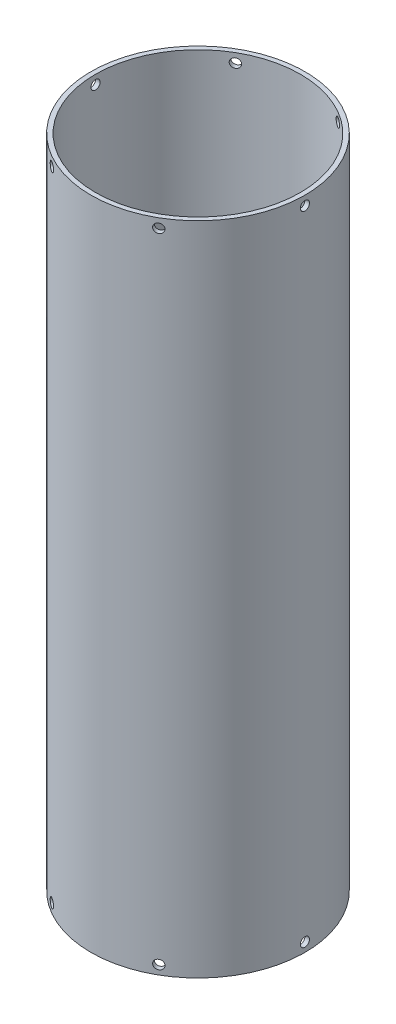
SolidWorks part; units mm, degrees
material "6061-T6 (SS)"
ref_plane "Front Plane" through (0, 0, 0) normal (0, 0, 1) x (1, 0, 0)
ref_plane "Top Plane" through (0, 0, 0) normal (0, 1, 0) x (1, 0, 0)
ref_plane "Right Plane" through (0, 0, 0) normal (1, 0, 0) x (0, 0, -1)
sketch "Sketch1" plane through (0, 0, 0) normal (0, 1, 0) x (1, 0, 0)
  circle A0 centre (0, 0) radius 142.875
  circle A1 centre (0, 0) radius 149.225
  dimension "D1" = 285.75
  dimension "D2" = 298.45
extrude "Boss-Extrude1" add sketch "Sketch1" along normal blind 914.4
ref_plane "Plane1" through (149.225, 0, 0) normal (1, 0, 0) x (0, 0, -1)
hole_wizard "1/2 (0.5) Diameter Hole1" positions "Sketch2" profile "Sketch4" hole size "1/2" standard "ANSI Inch"
sketch "Sketch2" plane through (149.225, 0, 0) normal (1, 0, 0) x (0, 0, -1)
  line L0 (149.225, 914.4) -> (-149.225, 914.4) construction
  line L1 (0, 164.1475) -> (0, -164.1475) construction
  point P0 (0, 901.7)
  dimension "D1" = 12.7
sketch "Sketch4" plane through (149.225, 901.7, 0) normal (0, 1, 0) x (0, 0, -1)
  line L0 (0, 0) -> (0, 344.3972)
  line L1 (0, 344.3972) -> (6.35, 344.3972)
  line L2 (6.35, 344.3972) -> (6.35, 0)
  line L5 (6.35, 0) -> (0, 0)
  line L11 (0, -6.35) -> (0, 107.95) construction
  dimension "Thru Hole Dia." = 12.7
  dimension "Thru Hole Depth" = 344.3972
pattern_circular "CirPattern1" count 6 over 360 about axis through (0, 914.4, 0) along (0, 1, 0) of "1/2 (0.5) Diameter Hole1"
ref_plane "Plane2" through (0, 457.2, 0) normal (0, -1, 0) x (-1, 0, 0)
mirror "Mirror1" about plane through (0, 457.2, 0) normal (0, -1, 0) of "CirPattern1", "1/2 (0.5) Diameter Hole1"
